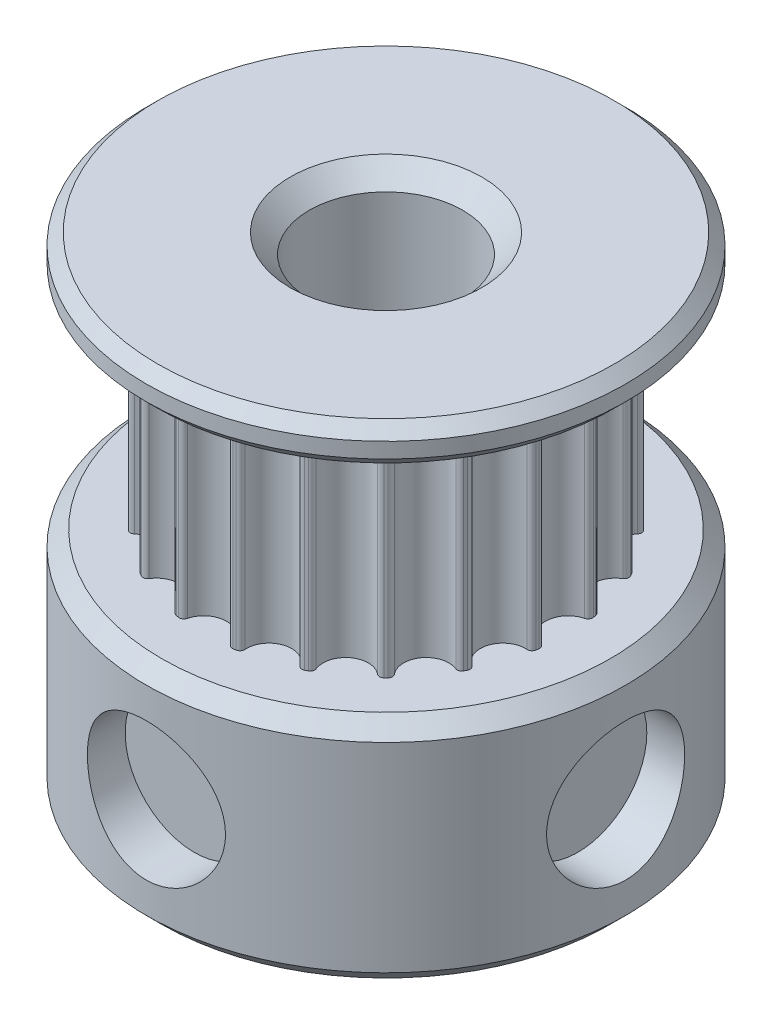
SolidWorks part; units mm, degrees
ref_plane "Front Plane" through (0, 0, 0) normal (0, 0, 1) x (1, 0, 0)
ref_plane "Top Plane" through (0, 0, 0) normal (0, 1, 0) x (1, 0, 0)
ref_plane "Right Plane" through (0, 0, 0) normal (1, 0, 0) x (0, 0, -1)
ref_plane "Plane1" through (0, 0, 0) normal (0, 0, -1) x (-1, 0, 0)
sketch "Sketch1" plane through (0, 0, 0) normal (0, 0, -1) x (-1, 0, 0)
  line L0 (-7.5565, 14.859) -> (0, 14.859)
  line L1 (0, 14.859) -> (0, 16.129)
  line L2 (0, 16.129) -> (-7.5565, 16.129)
  line L3 (-7.5565, 16.129) -> (-7.9375, 15.748)
  line L4 (-7.9375, 15.748) -> (-7.9375, 15.24)
  line L5 (-7.9375, 15.24) -> (-7.5565, 14.859)
  line L6 (0, 14.859) -> (0, 16.129) construction
revolve "Revolve1" add sketch "Sketch1" angle 360 about L6
sketch "Sketch2" plane through (0, 14.859, 0) normal (0, -1, 0) x (1, 0, 0)
  arc A0 (4.3011, 4.2298) -> (4.4027, 4.124) centre (0, 0) cw
  arc A1 (4.4027, 4.124) -> (5.2827, 2.9128) centre (4.8804, 3.5458) ccw
  arc A2 (5.2827, 2.9128) -> (5.3519, 2.7835) centre (0, 0) cw
  arc A3 (5.3977, 2.6937) -> (5.4616, 2.5617) centre (0, 0) cw
  arc A4 (5.4616, 2.5617) -> (5.9242, 1.1378) centre (5.7372, 1.8641) ccw
  arc A5 (5.9242, 1.1378) -> (5.9501, 0.9934) centre (0, 0) cw
  arc A6 (5.9659, 0.8939) -> (5.9859, 0.7485) centre (0, 0) cw
  arc A7 (5.9859, 0.7485) -> (5.9859, -0.7485) centre (6.0325, 0) ccw
  arc A8 (5.9859, -0.7485) -> (5.9659, -0.8939) centre (0, 0) cw
  arc A9 (5.9501, -0.9934) -> (5.9242, -1.1378) centre (0, 0) cw
  arc A10 (5.9242, -1.1378) -> (5.4616, -2.5617) centre (5.7372, -1.8641) ccw
  arc A11 (5.4616, -2.5617) -> (5.3977, -2.6937) centre (0, 0) cw
  arc A12 (5.3519, -2.7835) -> (5.2827, -2.9128) centre (0, 0) cw
  arc A13 (5.2827, -2.9128) -> (4.4027, -4.124) centre (4.8804, -3.5458) ccw
  arc A14 (4.4027, -4.124) -> (4.3011, -4.2298) centre (0, 0) cw
  arc A15 (4.2298, -4.3011) -> (4.124, -4.4027) centre (0, 0) cw
  arc A16 (4.124, -4.4027) -> (2.9128, -5.2827) centre (3.5458, -4.8804) ccw
  arc A17 (2.9128, -5.2827) -> (2.7835, -5.3519) centre (0, 0) cw
  arc A18 (2.6937, -5.3977) -> (2.5617, -5.4616) centre (0, 0) cw
  arc A19 (2.5617, -5.4616) -> (1.1378, -5.9242) centre (1.8641, -5.7372) ccw
  arc A20 (1.1378, -5.9242) -> (0.9934, -5.9501) centre (0, 0) cw
  arc A21 (0.8939, -5.9659) -> (0.7485, -5.9859) centre (0, 0) cw
  arc A22 (0.7485, -5.9859) -> (-0.7485, -5.9859) centre (0, -6.0325) ccw
  arc A23 (-0.7485, -5.9859) -> (-0.8939, -5.9659) centre (0, 0) cw
  arc A24 (-0.9934, -5.9501) -> (-1.1378, -5.9242) centre (0, 0) cw
  arc A25 (-1.1378, -5.9242) -> (-2.5617, -5.4616) centre (-1.8641, -5.7372) ccw
  arc A26 (-2.5617, -5.4616) -> (-2.6937, -5.3977) centre (0, 0) cw
  arc A27 (-2.7835, -5.3519) -> (-2.9128, -5.2827) centre (0, 0) cw
  arc A28 (-2.9128, -5.2827) -> (-4.124, -4.4027) centre (-3.5458, -4.8804) ccw
  arc A29 (-4.124, -4.4027) -> (-4.2298, -4.3011) centre (0, 0) cw
  arc A30 (-4.3011, -4.2298) -> (-4.4027, -4.124) centre (0, 0) cw
  arc A31 (-4.4027, -4.124) -> (-5.2827, -2.9128) centre (-4.8804, -3.5458) ccw
  arc A32 (-5.2827, -2.9128) -> (-5.3519, -2.7835) centre (0, 0) cw
  arc A33 (-5.3977, -2.6937) -> (-5.4616, -2.5617) centre (0, 0) cw
  arc A34 (-5.4616, -2.5617) -> (-5.9242, -1.1378) centre (-5.7372, -1.8641) ccw
  arc A35 (-5.9242, -1.1378) -> (-5.9501, -0.9934) centre (0, 0) cw
  arc A36 (-5.9659, -0.8939) -> (-5.9859, -0.7485) centre (0, 0) cw
  arc A37 (-5.9859, -0.7485) -> (-5.9859, 0.7485) centre (-6.0325, 0) ccw
  arc A38 (-5.9859, 0.7485) -> (-5.9659, 0.8939) centre (0, 0) cw
  arc A39 (-5.9501, 0.9934) -> (-5.9242, 1.1378) centre (0, 0) cw
  arc A40 (-5.9242, 1.1378) -> (-5.4616, 2.5617) centre (-5.7372, 1.8641) ccw
  arc A41 (-5.4616, 2.5617) -> (-5.3977, 2.6937) centre (0, 0) cw
  arc A42 (-5.3519, 2.7835) -> (-5.2827, 2.9128) centre (0, 0) cw
  arc A43 (-5.2827, 2.9128) -> (-4.4027, 4.124) centre (-4.8804, 3.5458) ccw
  arc A44 (-4.4027, 4.124) -> (-4.3011, 4.2298) centre (0, 0) cw
  arc A45 (-4.2298, 4.3011) -> (-4.124, 4.4027) centre (0, 0) cw
  arc A46 (-4.124, 4.4027) -> (-2.9128, 5.2827) centre (-3.5458, 4.8804) ccw
  arc A47 (-2.9128, 5.2827) -> (-2.7835, 5.3519) centre (0, 0) cw
  arc A48 (-2.6937, 5.3977) -> (-2.5617, 5.4616) centre (0, 0) cw
  arc A49 (-2.5617, 5.4616) -> (-1.1378, 5.9242) centre (-1.8641, 5.7372) ccw
  arc A50 (-1.1378, 5.9242) -> (-0.9934, 5.9501) centre (0, 0) cw
  arc A51 (-0.8939, 5.9659) -> (-0.7485, 5.9859) centre (0, 0) cw
  arc A52 (-0.7485, 5.9859) -> (0.7485, 5.9859) centre (0, 6.0325) ccw
  arc A53 (0.7485, 5.9859) -> (0.8939, 5.9659) centre (0, 0) cw
  arc A54 (0.9934, 5.9501) -> (1.1378, 5.9242) centre (0, 0) cw
  arc A55 (1.1378, 5.9242) -> (2.5617, 5.4616) centre (1.8641, 5.7372) ccw
  arc A56 (2.5617, 5.4616) -> (2.6937, 5.3977) centre (0, 0) cw
  arc A57 (2.7835, 5.3519) -> (2.9128, 5.2827) centre (0, 0) cw
  arc A58 (2.9128, 5.2827) -> (4.124, 4.4027) centre (3.5458, 4.8804) ccw
  arc A59 (4.124, 4.4027) -> (4.2298, 4.3011) centre (0, 0) cw
  spline S0 degree 3 poles (5.3977, 2.6937) (5.3827, 2.7238) (5.3674, 2.7537) (5.3519, 2.7835) knots 0 0 0 0 1 1 1 1
  spline S1 degree 3 poles (5.9659, 0.8939) (5.9609, 0.9271) (5.9557, 0.9603) (5.9501, 0.9934) knots 0 0 0 0 1 1 1 1
  spline S2 degree 3 poles (5.9501, -0.9934) (5.9557, -0.9603) (5.9609, -0.9271) (5.9659, -0.8939) knots 0 0 0 0 1 1 1 1
  spline S3 degree 3 poles (5.3519, -2.7835) (5.3674, -2.7537) (5.3827, -2.7238) (5.3977, -2.6937) knots 0 0 0 0 1 1 1 1
  spline S4 degree 3 poles (4.2298, -4.3011) (4.2538, -4.2775) (4.2775, -4.2538) (4.3011, -4.2298) knots 0 0 0 0 1 1 1 1
  spline S5 degree 3 poles (2.6937, -5.3977) (2.7238, -5.3827) (2.7537, -5.3674) (2.7835, -5.3519) knots 0 0 0 0 1 1 1 1
  spline S6 degree 3 poles (0.8939, -5.9659) (0.9271, -5.9609) (0.9603, -5.9557) (0.9934, -5.9501) knots 0 0 0 0 1 1 1 1
  spline S7 degree 3 poles (-0.9934, -5.9501) (-0.9603, -5.9557) (-0.9271, -5.9609) (-0.8939, -5.9659) knots 0 0 0 0 1 1 1 1
  spline S8 degree 3 poles (-2.7835, -5.3519) (-2.7537, -5.3674) (-2.7238, -5.3827) (-2.6937, -5.3977) knots 0 0 0 0 1 1 1 1
  spline S9 degree 3 poles (-4.3011, -4.2298) (-4.2775, -4.2538) (-4.2538, -4.2775) (-4.2298, -4.3011) knots 0 0 0 0 1 1 1 1
  spline S10 degree 3 poles (-5.3977, -2.6937) (-5.3827, -2.7238) (-5.3674, -2.7537) (-5.3519, -2.7835) knots 0 0 0 0 1 1 1 1
  spline S11 degree 3 poles (-5.9659, -0.8939) (-5.9609, -0.9271) (-5.9557, -0.9603) (-5.9501, -0.9934) knots 0 0 0 0 1 1 1 1
  spline S12 degree 3 poles (-5.9501, 0.9934) (-5.9557, 0.9603) (-5.9609, 0.9271) (-5.9659, 0.8939) knots 0 0 0 0 1 1 1 1
  spline S13 degree 3 poles (-5.3519, 2.7835) (-5.3674, 2.7537) (-5.3827, 2.7238) (-5.3977, 2.6937) knots 0 0 0 0 1 1 1 1
  spline S14 degree 3 poles (-4.2298, 4.3011) (-4.2538, 4.2775) (-4.2775, 4.2538) (-4.3011, 4.2298) knots 0 0 0 0 1 1 1 1
  spline S15 degree 3 poles (-2.6937, 5.3977) (-2.7238, 5.3827) (-2.7537, 5.3674) (-2.7835, 5.3519) knots 0 0 0 0 1 1 1 1
  spline S16 degree 3 poles (-0.8939, 5.9659) (-0.9271, 5.9609) (-0.9603, 5.9557) (-0.9934, 5.9501) knots 0 0 0 0 1 1 1 1
  spline S17 degree 3 poles (0.9934, 5.9501) (0.9603, 5.9557) (0.9271, 5.9609) (0.8939, 5.9659) knots 0 0 0 0 1 1 1 1
  spline S18 degree 3 poles (2.7835, 5.3519) (2.7537, 5.3674) (2.7238, 5.3827) (2.6937, 5.3977) knots 0 0 0 0 1 1 1 1
  spline S19 degree 3 poles (4.3011, 4.2298) (4.2775, 4.2538) (4.2538, 4.2775) (4.2298, 4.3011) knots 0 0 0 0 1 1 1 1
extrude "Boss-Extrude1" add sketch "Sketch2" along normal blind 7.239
ref_plane "Plane2" through (0, 7.62, 0) normal (0, 1, 0) x (1, 0, 0)
sketch "Sketch3" plane through (0, 7.62, 0) normal (0, 1, 0) x (1, 0, 0)
  circle A0 centre (0, 0) radius 7.9375
extrude "Boss-Extrude2" add sketch "Sketch3" against normal blind 7.62
hole_wizard "M4 Clearance Hole1" positions "3DSketch1" profile "Sketch4" hole size "M4" standard "ANSI Metric"
sketch3d "3DSketch1"
  point P0 (7.9375, 3.81, 0)
sketch "Sketch4" plane through (7.9375, 3.81, 0) normal (0, 1, 0) x (0, 0, -1)
  line L0 (0, 0) -> (0, 1.5875)
  line L1 (0, 1.5875) -> (2.286, 1.5875)
  line L2 (2.286, 1.5875) -> (2.286, 0)
  line L5 (2.286, 0) -> (0, 0)
  line L10 (0, 1.5875) -> (-2.286, 1.5875) construction
  line L11 (0, -6.35) -> (0, 107.95) construction
  dimension "Hole Dia." = 4.572
  dimension "Hole Depth" = 1.5875
  dimension "Drill Angle" = 180
hole_wizard "M4 Clearance Hole2" positions "3DSketch2" profile "Sketch5" hole size "M4" standard "ANSI Metric"
sketch3d "3DSketch2"
  point P0 (0, 3.81, 7.9375)
sketch "Sketch5" plane through (0, 3.81, 7.9375) normal (1, 0, 0) x (0, -1, 0)
  line L0 (0, 0) -> (0, 1.5875)
  line L1 (0, 1.5875) -> (2.286, 1.5875)
  line L2 (2.286, 1.5875) -> (2.286, 0)
  line L5 (2.286, 0) -> (0, 0)
  line L10 (0, 1.5875) -> (-2.286, 1.5875) construction
  line L11 (0, -6.35) -> (0, 107.95) construction
  dimension "Hole Dia." = 4.572
  dimension "Hole Depth" = 1.5875
  dimension "Drill Angle" = 180
hole_wizard "Hole1" positions "Sketch7" profile "Sketch6" legacy
sketch "Sketch7" plane through (0, 0, 0) normal (0, -1, 0) x (-1, 0, 0)
  point P0 (0, 0)
sketch "Sketch6" plane through (0, 0, 0) normal (1, 0, 0) x (0, 0, -1)
  line L0 (0, 0) -> (0, 16.129)
  line L1 (0, 16.129) -> (2.54, 16.129)
  line L2 (2.54, 16.129) -> (2.54, 0)
  line L3 (2.54, 0) -> (0, 0)
  line L4 (0, 110) -> (0, -10) construction
  dimension "Diameter" = 5.08
  dimension "Depth" = 16.129
chamfer "Chamfer1" distance 0.635 angle 45 2 edges at (0, 16.129, -2.54) (0, 0, -2.54)
chamfer "Chamfer2" distance 0.508 angle 45 2 edges at (0, 0, -7.9375) (0, 7.62, -7.9375)
fillet "Fillet1" radius 0.152 40 edges at (4.124, 11.2395, -4.4027) (-2.9128, 11.2395, -5.2827) (5.4616, 11.2395, 2.5617) (5.2827, 11.2395, 2.9128) (0.7485, 11.2395, -5.9859) (4.4027, 11.2395, 4.124) (5.9242, 11.2395, -1.1378) (4.124, 11.2395, 4.4027) (-4.4027, 11.2395, -4.124) (2.9128, 11.2395, 5.2827) (-1.1378, 11.2395, -5.9242) (2.5617, 11.2395, 5.4616) (2.5617, 11.2395, -5.4616) (1.1378, 11.2395, 5.9242) (5.2827, 11.2395, -2.9128) (0.7485, 11.2395, 5.9859) (5.9859, 11.2395, 0.7485) (-0.7485, 11.2395, 5.9859) (-5.2827, 11.2395, -2.9128) (-1.1378, 11.2395, 5.9242) (-4.124, 11.2395, -4.4027) (-2.5617, 11.2395, 5.4616) (-2.5617, 11.2395, -5.4616) (-2.9128, 11.2395, 5.2827) (-0.7485, 11.2395, -5.9859) (-4.124, 11.2395, 4.4027) (1.1378, 11.2395, -5.9242) (-4.4027, 11.2395, 4.124) (2.9128, 11.2395, -5.2827) (-5.2827, 11.2395, 2.9128) (4.4027, 11.2395, -4.124) (-5.4616, 11.2395, 2.5617) (5.4616, 11.2395, -2.5617) (-5.9242, 11.2395, 1.1378) (5.9859, 11.2395, -0.7485) (-5.9859, 11.2395, 0.7485) (5.9242, 11.2395, 1.1378) (-5.9242, 11.2395, -1.1378) (-5.4616, 11.2395, -2.5617) (-5.9859, 11.2395, -0.7485)
